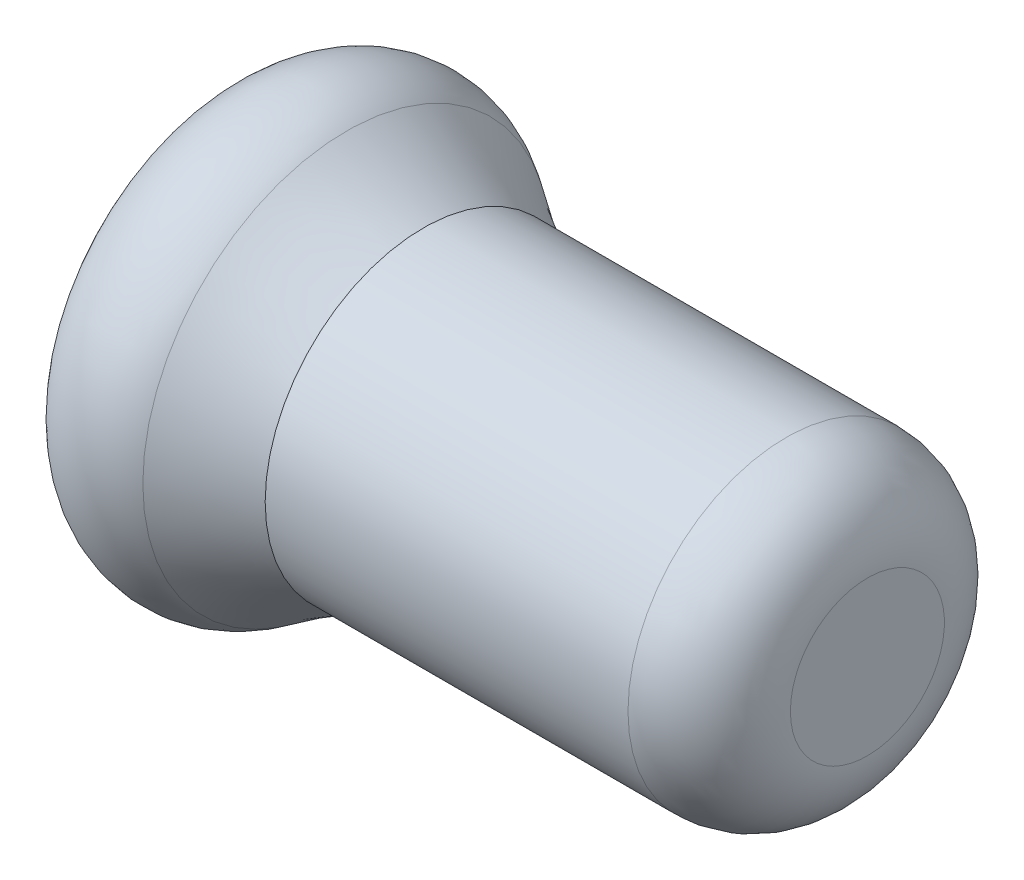
SolidWorks part; units mm, degrees
material "Polyethylene Cross-Linked"
ref_plane "Front" through (0, 0, 0) normal (0, 0, 1) x (1, 0, 0)
ref_plane "Top" through (0, 0, 0) normal (0, 1, 0) x (1, 0, 0)
ref_plane "Right" through (0, 0, 0) normal (1, 0, 0) x (0, 0, -1)
sketch "Sketch1" plane through (0, 0, 0) normal (0, 0, 1) x (1, 0, 0)
  line L1 (26.6806, 2) -> (26.6806, 0)
  line L2 (26.6806, 0) -> (21.6806, 0)
  line L3 (21.6806, 0) -> (21.6806, 2.5)
  line L4 (21.6806, 2.5) -> (-13.3194, 2.5)
  line L5 (-13.3194, 2.5) -> (-13.2943, 9)
  line L6 (-0.6564, 9.7406) -> (21.6806, 9.7406)
  line L7 (26.6806, 2) -> (26.6806, 4.7406)
  line L8 (-16.0092, 0) -> (32.4976, 0) construction
  arc A0 (-13.2943, 9) -> (-5.3835, 12.5473) centre (-8.3194, 8.5) cw
  arc A1 (-5.3835, 12.5473) -> (-0.6564, 9.7406) centre (12.2318, 36.8311) ccw
  arc A2 (21.6806, 9.7406) -> (26.6806, 4.7406) centre (21.6806, 4.7406) cw
  dimension "D6" = 5
  dimension "D8" = 5
  dimension "D1" = 6.5
  dimension "D2" = 35
  dimension "D3" = 5
  dimension "D4" = 2.5
  dimension "D5" = 2
  dimension "D7" = 30
  dimension "D9" = 2.2406
  dimension "D10" = 2.7406
  dimension "D11" = 7.2406
  dimension "D12" = 0.5
  dimension "D13" = 39.9911
  dimension "D14" = 10.0473
revolve "Revolve1" add sketch "Sketch1" angle 360 about L8
